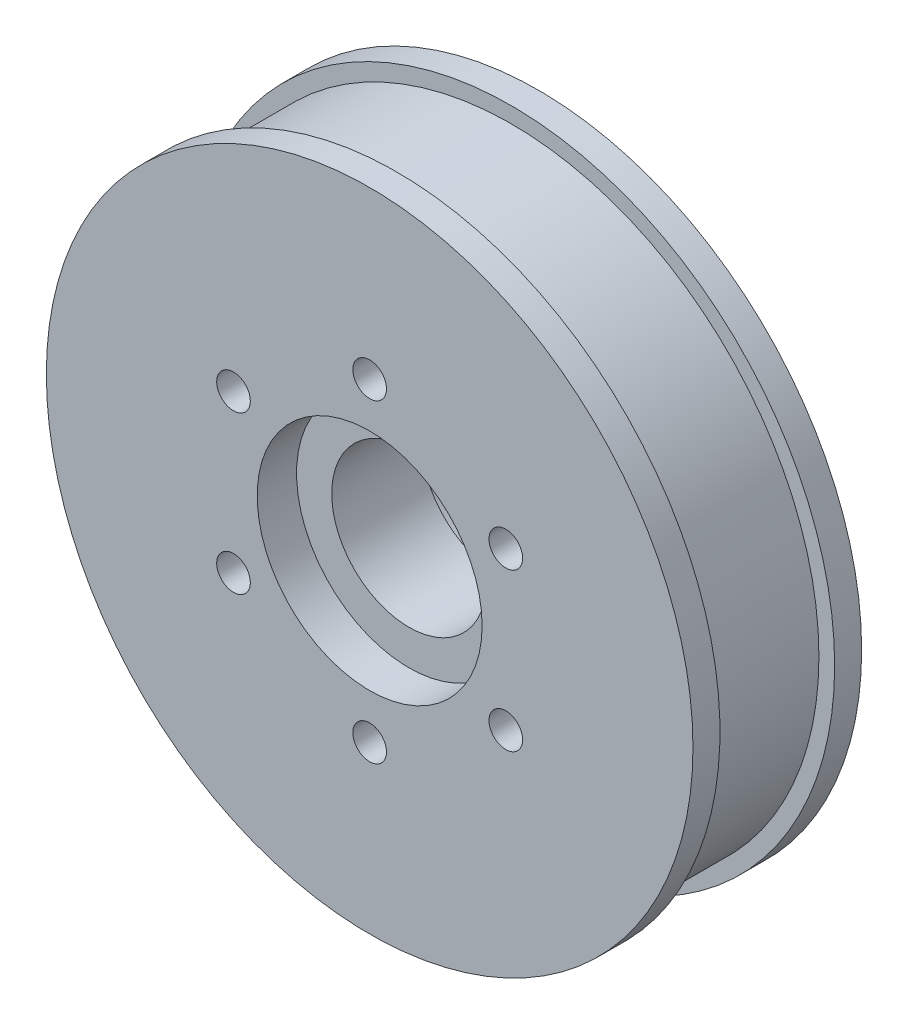
SolidWorks part; units mm, degrees
ref_plane "Front Plane" through (0, 0, 0) normal (0, 0, 1) x (1, 0, 0)
ref_plane "Top Plane" through (0, 0, 0) normal (0, 1, 0) x (1, 0, 0)
ref_plane "Right Plane" through (0, 0, 0) normal (1, 0, 0) x (0, 0, -1)
sketch "Sketch1" plane through (0, 0, 0) normal (0, 0, 1) x (1, 0, 0)
  circle A0 centre (0, 0) radius 36.5125
  dimension "D1" = 73.025
extrude "Boss-Extrude1" add sketch "Sketch1" along normal blind 19.05
sketch "Sketch2" plane through (0, 0, 19.05) normal (0, 0, 1) x (1, 0, 0)
  circle A0 centre (0, 0) radius 8.7312
  dimension "D1" = 17.4625
extrude "Cut-Extrude1" cut sketch "Sketch2" against normal through all
sketch "Sketch3" plane through (0, 0, 19.05) normal (0, 0, 1) x (1, 0, 0)
  circle A0 centre (0, 0) radius 12.7
  dimension "D1" = 25.4
extrude "Cut-Extrude2" cut sketch "Sketch3" against normal blind 4.445
sketch "Sketch4" plane through (0, 0, 0) normal (0, 0, -1) x (-1, 0, 0)
  circle A0 centre (0, 0) radius 12.7
  dimension "D1" = 25.4
extrude "Cut-Extrude3" cut sketch "Sketch4" against normal blind 4.445
sketch "Sketch5" plane through (0, 0, 0) normal (0, 0, -1) x (-1, 0, 0)
  line L0 (0, 0) -> (0, 50.3412)
  line L1 (0, 34.29) -> (2.1586, 36.4486)
  line L2 (0, 34.29) -> (-2.1586, 36.4486)
  circle A0 centre (0, 0) radius 36.5125
  circle A1 centre (0, 0) radius 34.29
  circle A2 centre (0, 0) radius 36.5125 construction
  circle M404 centre (0, 0) radius 36.5125
  dimension "D1" = 68.58
  dimension "D2" = 0
  dimension "D3" = 45
extrude "Cut-Extrude4" [suppressed] cut sketch "Sketch5" against normal through all contours L2 L0 M404 | L0 L1 M404
pattern_circular "CirPattern1" [suppressed] count 45 over 360
hole_wizard "#6 Clearance Hole1" positions "Sketch8" profile "Sketch9" hole size "#6" standard "ANSI Inch" end condition through all
sketch "Sketch8" plane through (-8.1703, -47.0035, 19.05) normal (0, 0, 1) x (1, 0, 0)
  point P0 (8.1703, 64.7581)
  point P1 (-7.2056, 55.8808)
  point P2 (-7.2056, 38.1262)
  point P4 (8.1703, 29.2489)
  point P6 (23.5462, 38.1262)
  point P8 (23.5462, 55.8808)
sketch "Sketch9" plane through (0, 17.7546, 19.05) normal (1, 0, 0) x (0, -1, 0)
  line L0 (0, 0) -> (0, 19.05)
  line L1 (0, 19.05) -> (1.8986, 19.05)
  line L2 (1.8986, 19.05) -> (1.8986, 0)
  line L5 (1.8986, 0) -> (0, 0)
  line L11 (0, -6.35) -> (0, 107.95) construction
  dimension "Thru Hole Dia." = 3.7973
  dimension "Thru Hole Depth" = 19.05
sketch "Sketch10" plane through (0, 0, 0) normal (1, 0, 0) x (0, 0, -1)
  line L0 (-19.05, 36.5125) -> (-16.002, 36.5125)
  line L1 (0, 36.5125) -> (-19.05, 36.5125) construction
  line L2 (-16.002, 36.5125) -> (-16.002, 34.7345)
  line L3 (-16.002, 34.7345) -> (-3.048, 34.7345)
  line L4 (-3.048, 34.7345) -> (-3.048, 36.5125)
  line L5 (-3.048, 36.5125) -> (0, 36.5125)
  line L6 (0, -36.5125) -> (0, 36.5125) construction
  line L8 (-19.05, 0) -> (0, 0)
  line L11 (-3.048, 36.5125) -> (-3.048, 51.1522)
  line L12 (-3.048, 51.1522) -> (-16.002, 51.1522)
  line L13 (-16.002, 51.1522) -> (-16.002, 36.5125)
  dimension "D1" = 3.048
  dimension "D2" = 3.048
  dimension "D3" = 1.778
revolve "Cut-Revolve1" cut sketch "Sketch10" angle 360 about L8
